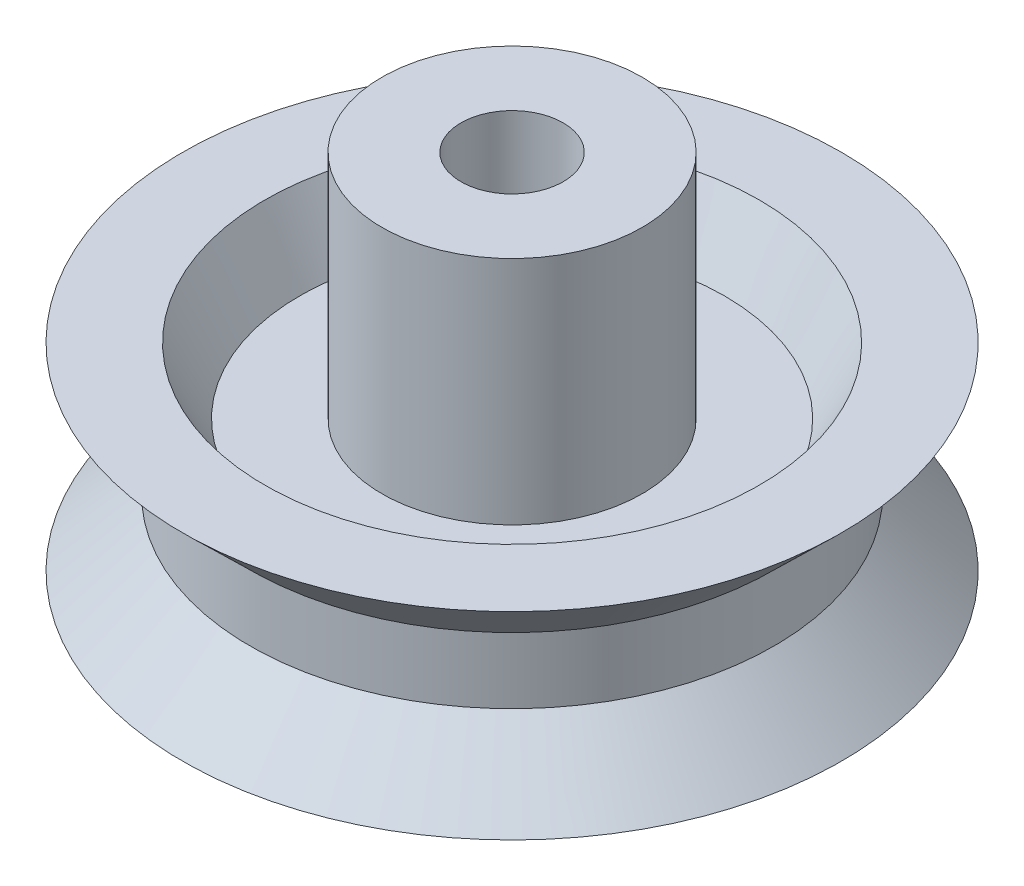
SolidWorks part; units mm, degrees
ref_plane "Plan de face" through (0, 0, 0) normal (0, 0, 1) x (1, 0, 0)
ref_plane "Plan de dessus" through (0, 0, 0) normal (0, 1, 0) x (1, 0, 0)
ref_plane "Plan de droite" through (0, 0, 0) normal (1, 0, 0) x (0, 0, -1)
sketch "Esquisse2" plane through (0, 0, 0) normal (1, 0, 0) x (0, 0, -1)
  line L0 (0, -10.3546) -> (0, 29.8737) construction
  line L1 (-4.6494, 0) -> (20.1064, 0) construction
  line L2 (15.7349, 6) -> (-0.3684, 6) construction
  line L3 (-0.3684, 11) -> (20.1064, 11) construction
  line L4 (10, 7.1659) -> (10, -7.2287) construction
  line L5 (3.95, 17.0362) -> (3.95, -0.6744) construction
  line L6 (1.55, 14.4199) -> (1.55, -0.8469) construction
  line L7 (-4.6494, 4) -> (8.755, 4) construction
  line L8 (7.95, 14.6499) -> (7.95, -2.7445) construction
  line L9 (-4.6494, 2) -> (8.755, 2) construction
  line L10 (7.5, 6.9968) -> (7.5, -4.4408) construction
  line L11 (6.45, 8.7847) -> (6.45, -1.2782) construction
  line L12 (1.55, 0) -> (3.95, 0)
  line L13 (3.95, 0) -> (3.95, 2)
  line L14 (3.95, 2) -> (6.45, 2)
  line L15 (6.45, 2) -> (7.5, 0)
  line L16 (7.5, 0) -> (10, 0)
  line L17 (10, 0) -> (7.95, 2)
  line L18 (7.95, 2) -> (7.95, 4)
  line L19 (7.95, 4) -> (10, 6)
  line L20 (10, 6) -> (7.5, 6)
  line L21 (7.5, 6) -> (6.45, 4)
  line L22 (6.45, 4) -> (3.95, 4)
  line L23 (3.95, 4) -> (3.95, 11)
  line L24 (3.95, 11) -> (1.55, 11)
  line L25 (1.55, 11) -> (1.55, 0)
  dimension "D1" = 10
  dimension "D2" = 6
  dimension "D3" = 11
  dimension "D4" = 7.95
  dimension "D5" = 2
  dimension "D6" = 2
  dimension "D7" = 3.95
  dimension "D8" = 1.55
  dimension "D9" = 2.5
  dimension "D10" = 2.5
revolve "Révolution1" add sketch "Esquisse2" angle 360 about L0
